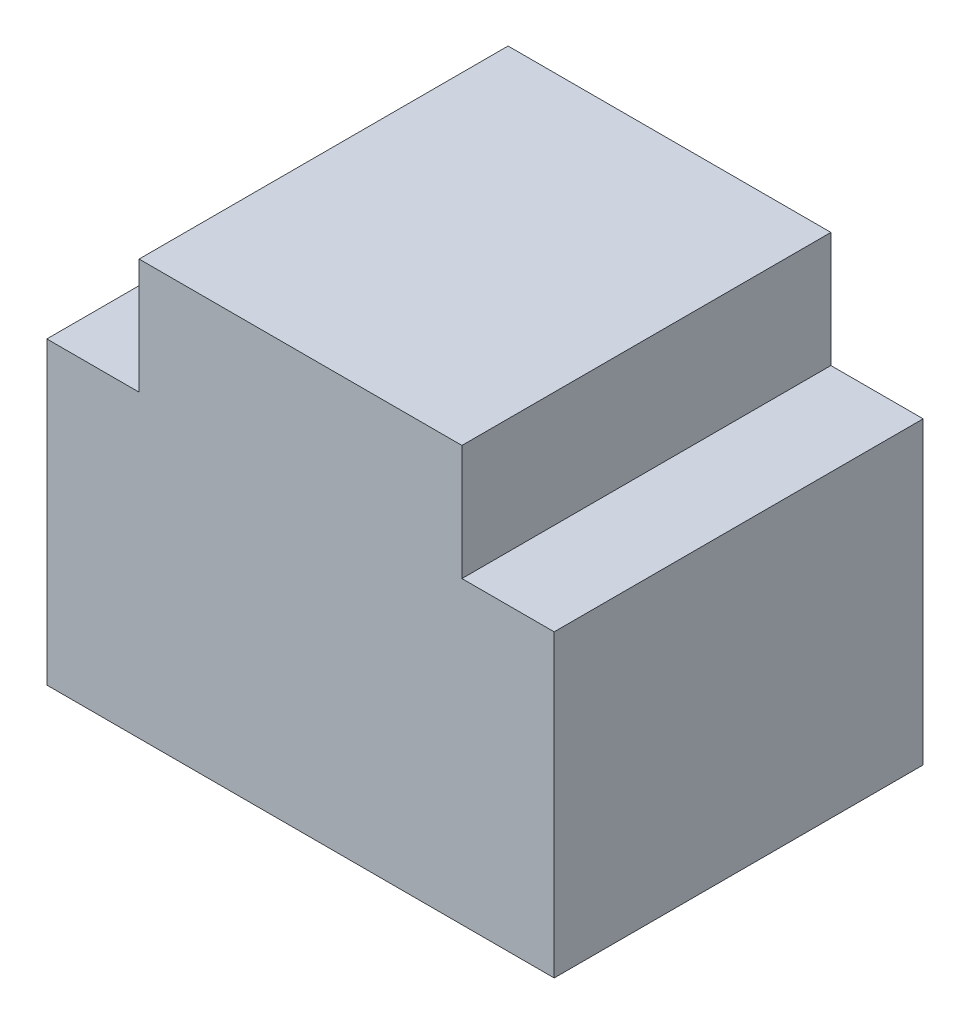
SolidWorks part; units mm, degrees
ref_plane "Front Plane" through (0, 0, 0) normal (0, 0, 1) x (1, 0, 0)
ref_plane "Top Plane" through (0, 0, 0) normal (0, 1, 0) x (1, 0, 0)
ref_plane "Right Plane" through (0, 0, 0) normal (1, 0, 0) x (0, 0, -1)
sketch "Sketch1" plane through (0, 0, 0) normal (0, 0, 1) x (1, 0, 0)
  line L0 (0, 0) -> (7, 0)
  line L1 (55, 0) -> (-55, 0) construction
  line L2 (7, 0) -> (7, -2.5)
  line L3 (7, -2.5) -> (9, -2.5)
  line L4 (9, -2.5) -> (9, -9)
  line L5 (9, -9) -> (-2, -9)
  line L6 (-2, -9) -> (-2, -2.5)
  line L7 (-2, -2.5) -> (0, -2.5)
  line L8 (0, -55) -> (0, 55) construction
  line L9 (0, -2.5) -> (0, 0)
  dimension "D1" = 2
  dimension "D2" = 11
extrude "Boss-Extrude1" add sketch "Sketch1" along normal blind 8
